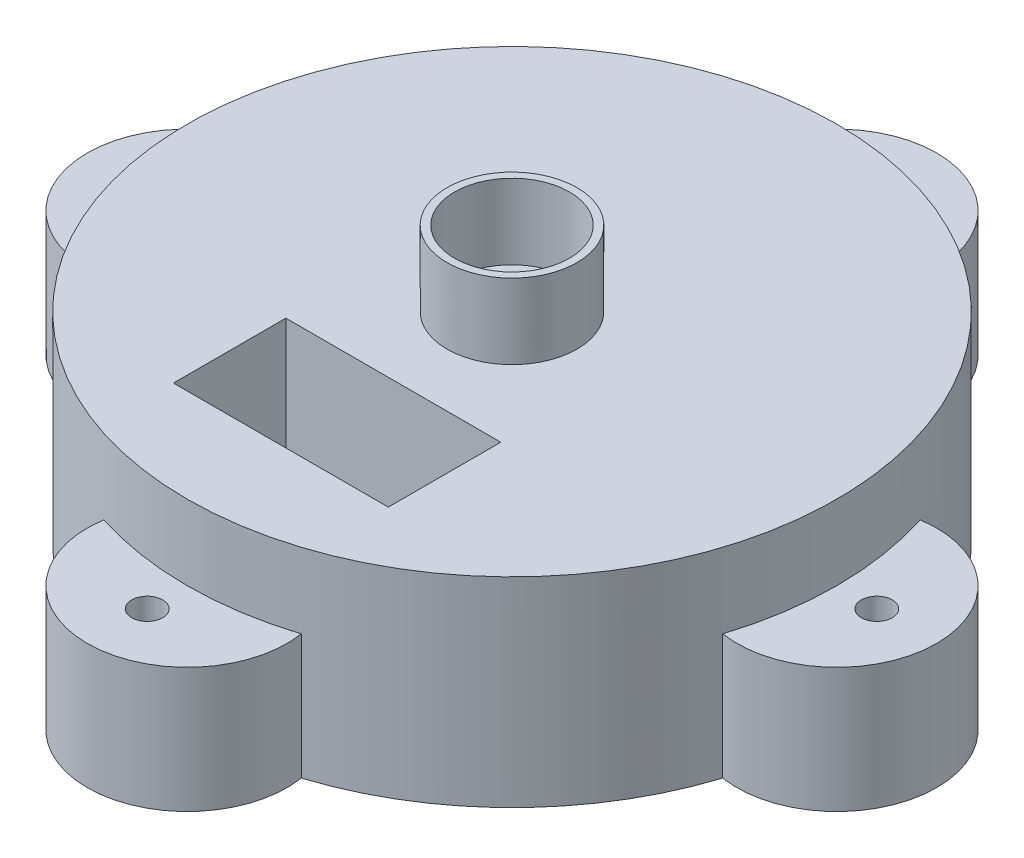
SolidWorks part; units mm, degrees
ref_plane "Front Plane" through (0, 0, 0) normal (0, 0, 1) x (1, 0, 0)
ref_plane "Top Plane" through (0, 0, 0) normal (0, 1, 0) x (1, 0, 0)
ref_plane "Right Plane" through (0, 0, 0) normal (1, 0, 0) x (0, 0, -1)
sketch "Sketch2" plane through (0, 0, 0) normal (0, 1, 0) x (1, 0, 0)
  circle A0 centre (0, 0) radius 65
  dimension "D1" = 130
extrude "Boss-Extrude1" add sketch "Sketch2" along normal blind 40
sketch "Sketch4" plane through (0, 40, 0) normal (0, -1, 0) x (1, 0, 0)
  line L1 (21.5, 23.75) -> (-21.5, 23.75)
  line L2 (21.5, 23.75) -> (21.5, 46.25)
  line L3 (21.5, 46.25) -> (-21.5, 46.25)
  line L4 (-21.5, 23.75) -> (-21.5, 46.25)
  line L5 (21.5, 23.75) -> (-21.5, 46.25) construction
  line L6 (21.5, 46.25) -> (-21.5, 23.75) construction
  point P0 (0, 35)
  dimension "D1" = 22.5
  dimension "D2" = 43
  dimension "D3" = 35
extrude "Cut-Extrude1" cut sketch "Sketch4" along normal blind 38
sketch "Sketch5" plane through (-21.5, 0, 62.75) normal (-1, 0, 0) x (0, 0, 1)
  line L6 (-19.2167, 7.326) -> (-34.2167, 7.326)
  line L7 (-19.2167, 7.326) -> (-19.2167, 12.326)
  line L8 (-19.2167, 12.326) -> (-34.2167, 12.326)
  line L9 (-34.2167, 7.326) -> (-34.2167, 12.326)
  line L10 (-19.2167, 7.326) -> (-34.2167, 12.326) construction
  line L11 (-19.2167, 12.326) -> (-34.2167, 7.326) construction
  point P0 (-62.75, 32)
  point P1 (-26.7167, 9.826)
  dimension "D1" = 15
  dimension "D2" = 5
sketch "Sketch6" plane through (0, 0, 0) normal (0, 1, 0) x (1, 0, 0)
  line L4 (-0.0001, -55) -> (-0.0001, -73) construction
  circle A2 centre (0, 0) radius 65 construction
  circle A3 centre (-0.0001, -73) radius 3.1
  arc A6 (-61.9231, 19.762) -> (-61.9231, -19.7618) centre (-65, 0.0001) ccw
  circle A8 centre (0, 0) radius 65
  circle A10 centre (0, 0) radius 65
  circle A12 centre (-73, 0.0001) radius 3.1
  arc A14 (-19.762, -61.9231) -> (19.7618, -61.9231) centre (-0.0001, -65) ccw
  arc A15 (19.762, 61.9231) -> (-19.7618, 61.9231) centre (0.0001, 65) ccw
  circle A16 centre (0.0001, 73) radius 3.1
  arc A17 (61.9231, -19.762) -> (61.9231, 19.7618) centre (65, -0.0001) ccw
  circle A18 centre (73, -0.0001) radius 3.1
  point P5 (-0.0001, -65)
  point P30 (0, 0)
  point P35 (0.4878, -1.815)
  dimension "D1" = 40
  dimension "D2" = 6.2
  dimension "D5" = 8
  dimension "D3" = 0
  dimension "D4" = 4
extrude "Boss-Extrude2" add sketch "Sketch6" along normal blind 25
sketch "Sketch9" plane through (0, 40, 0) normal (0, -1, 0) x (-1, 0, 0)
  circle A0 centre (0, 0) radius 13
  circle A2 centre (0, 0) radius 11.5
  dimension "D1" = 23
  dimension "23" = 26
extrude "Boss-Extrude3" add sketch "Sketch9" against normal blind 15
extrude "Cut-Extrude2" cut sketch "Sketch5" along normal blind 60
